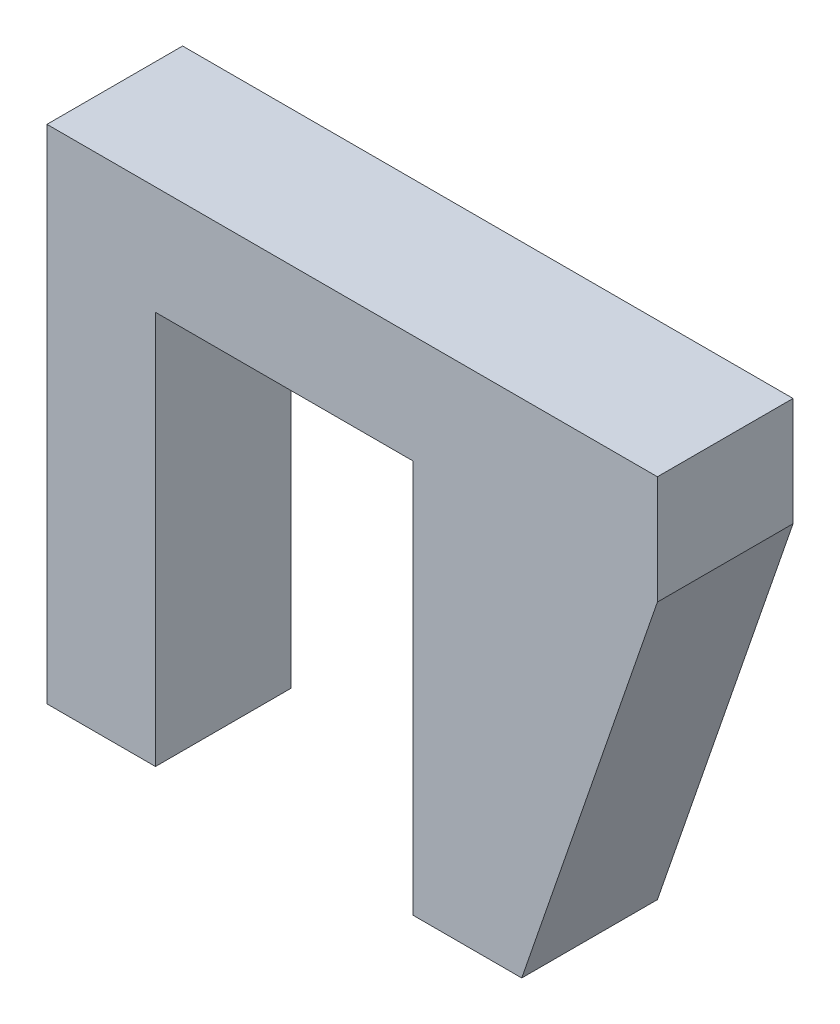
SolidWorks part; units mm, degrees
ref_plane "Front Plane" through (0, 0, 0) normal (0, 0, 1) x (1, 0, 0)
ref_plane "Top Plane" through (0, 0, 0) normal (0, 1, 0) x (1, 0, 0)
ref_plane "Right Plane" through (0, 0, 0) normal (1, 0, 0) x (0, 0, -1)
sketch "Sketch1" plane through (0, 0, 0) normal (0, 0, 1) x (1, 0, 0)
  line L0 (-4.75, -4.75) -> (-4.75, -9.75)
  line L1 (-4.75, -4.75) -> (4.75, -4.75) construction
  line L2 (-4.75, -4.75) -> (-4.75, 4.75)
  line L3 (-4.75, 4.75) -> (4.75, 4.75)
  line L4 (4.75, -4.75) -> (4.75, 4.75)
  line L5 (0, 4.75) -> (0, -4.75) construction
  line L6 (-4.75, 0) -> (4.75, 0) construction
  line L7 (-4.75, -9.75) -> (-8.75, -9.75)
  line L8 (-8.75, -9.75) -> (-8.75, 8.75)
  line L9 (-8.75, 8.75) -> (8.75, 8.75)
  line L10 (8.75, 8.75) -> (8.75, -9.75) construction
  line L11 (8.75, -9.75) -> (4.75, -9.75)
  line L12 (4.75, -9.75) -> (4.75, -4.75)
  line L15 (13.75, 4.75) -> (13.75, 8.75)
  line L16 (13.75, 8.75) -> (8.75, 8.75)
  line L17 (13.75, 4.75) -> (8.75, -9.75)
  point P0 (0, 0)
  dimension "D1" = 9.5
  dimension "D2" = 4
  dimension "D3" = 4
  dimension "D4" = 5
  dimension "D5" = 4
  dimension "D6" = 5
extrude "Boss-Extrude1" add sketch "Sketch1" along normal blind 5
